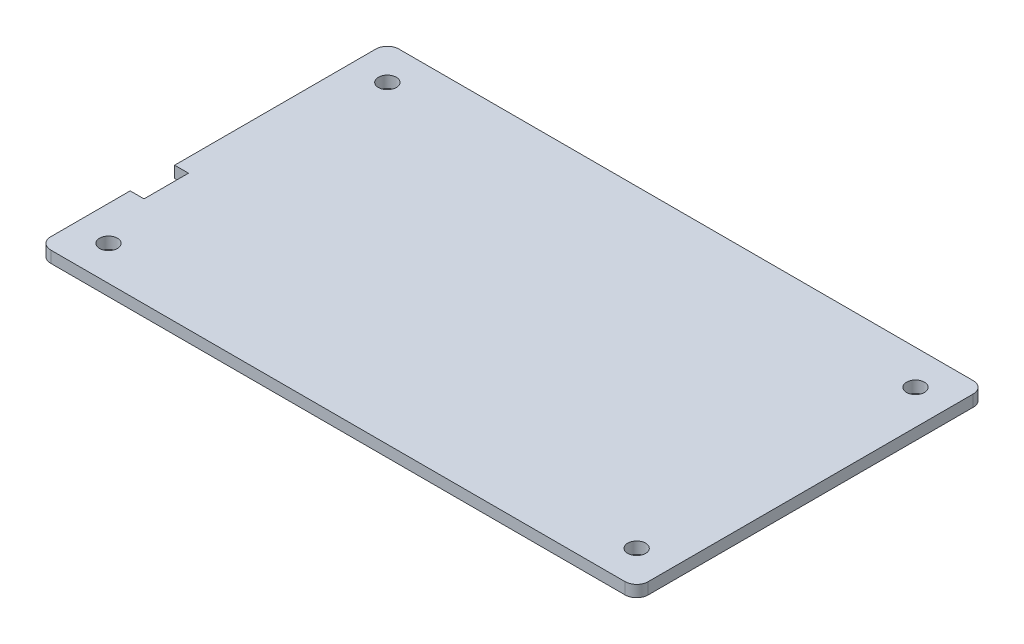
SolidWorks part; units mm, degrees
ref_plane "前视基准面" through (0, 0, 0) normal (0, 0, 1) x (1, 0, 0)
ref_plane "上视基准面" through (0, 0, 0) normal (0, 1, 0) x (1, 0, 0)
ref_plane "右视基准面" through (0, 0, 0) normal (1, 0, 0) x (0, 0, -1)
sketch "草图1" plane through (0, 0, 0) normal (0, 1, 0) x (1, 0, 0)
  line L0 (0, 0) -> (-12.7865, 0) construction
  line L1 (0, 0) -> (0, 22.3168) construction
  line L2 (91.46, 0) -> (91.46, 15.7584) construction
  line L3 (91.46, 48.29) -> (79.4981, 48.29) construction
  line L4 (-6, 0) -> (-6, 22.3168) construction
  line L5 (0, -6) -> (-12.7865, -6) construction
  line L6 (91.46, 54.29) -> (79.4981, 54.29) construction
  line L7 (97.46, 0) -> (97.46, 15.7584) construction
  line L8 (95.46, 54.29) -> (-4, 54.29)
  line L9 (-6, 52.29) -> (-6, -4)
  line L10 (-4, -6) -> (95.46, -6)
  line L11 (97.46, -4) -> (97.46, 52.29)
  line L12 (0, 9.75) -> (-12.7865, 9.75) construction
  line L13 (0, 17.45) -> (-12.7865, 17.45) construction
  line L14 (-3.6, 52.29) -> (-3.6, -4) construction
  line L16 (-6, 17.45) -> (-3.6, 17.45)
  line L17 (-6, 17.45) -> (-6, 9.75)
  line L18 (-6, 9.75) -> (-3.6, 9.75)
  line L19 (-3.6, 17.45) -> (-3.6, 9.75)
  circle A0 centre (0, 0) radius 1.55
  circle A1 centre (91.46, 0) radius 1.55
  circle A2 centre (91.46, 48.29) radius 1.55
  circle A3 centre (0, 48.29) radius 1.55
  circle A4 centre (-4, 52.29) radius 2
  circle A5 centre (-4, -4) radius 2
  circle A6 centre (95.46, -4) radius 2
  circle A7 centre (95.46, 52.29) radius 2
  dimension "D1" = 2
  dimension "D9" = 2.4
  dimension "D7" = 15.75
  dimension "D8" = 7.7
  dimension "D3" = 6
  dimension "D4" = 6
  dimension "D5" = 6
  dimension "D6" = 6
  dimension "D2" = 2
extrude "凸台-拉伸1" add sketch "草图1" along normal blind 2 contours A7 L8 A4 L9 A5 L10 A6 L11 A3 A2 A1 A0 | A5 | A4 | A7 | A6
